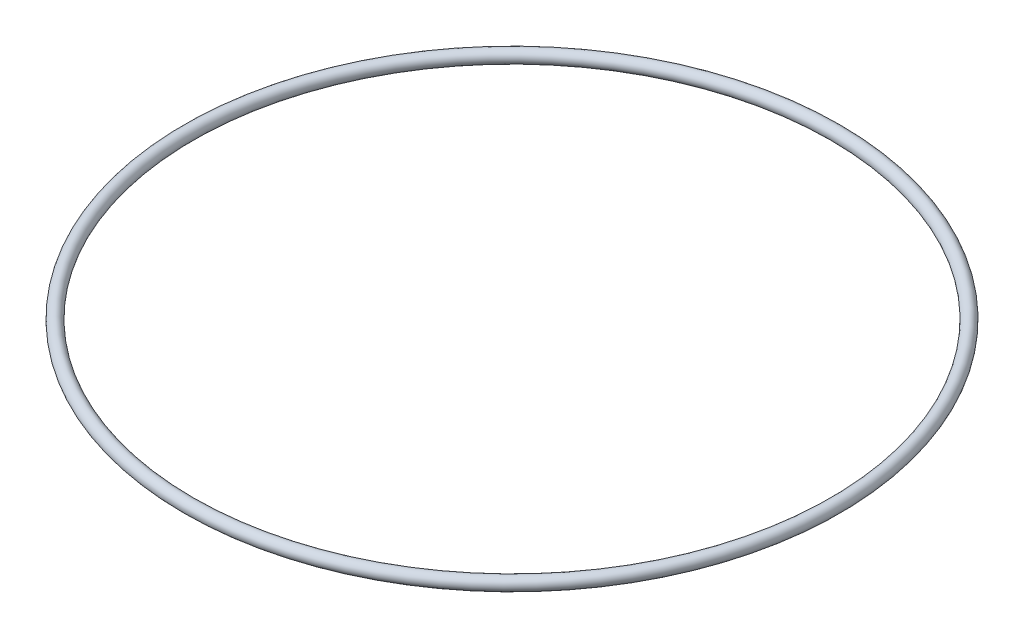
SolidWorks part; units mm, degrees
material "Rubber"
ref_plane "Front Plane" through (0, 0, 0) normal (0, 0, 1) x (1, 0, 0)
ref_plane "Top Plane" through (0, 0, 0) normal (0, 1, 0) x (1, 0, 0)
ref_plane "Right Plane" through (0, 0, 0) normal (1, 0, 0) x (0, 0, -1)
sketch "Sketch1" plane through (0, 0, 0) normal (0, 0, 1) x (1, 0, 0)
  line L0 (0, 0) -> (0, 4.6801) construction
  circle A0 centre (-41.91, 0) radius 0.8255
  dimension "D1" = 1.651
  dimension "D2" = 41.91
revolve "Revolve1" add sketch "Sketch1" angle 360 about L0
